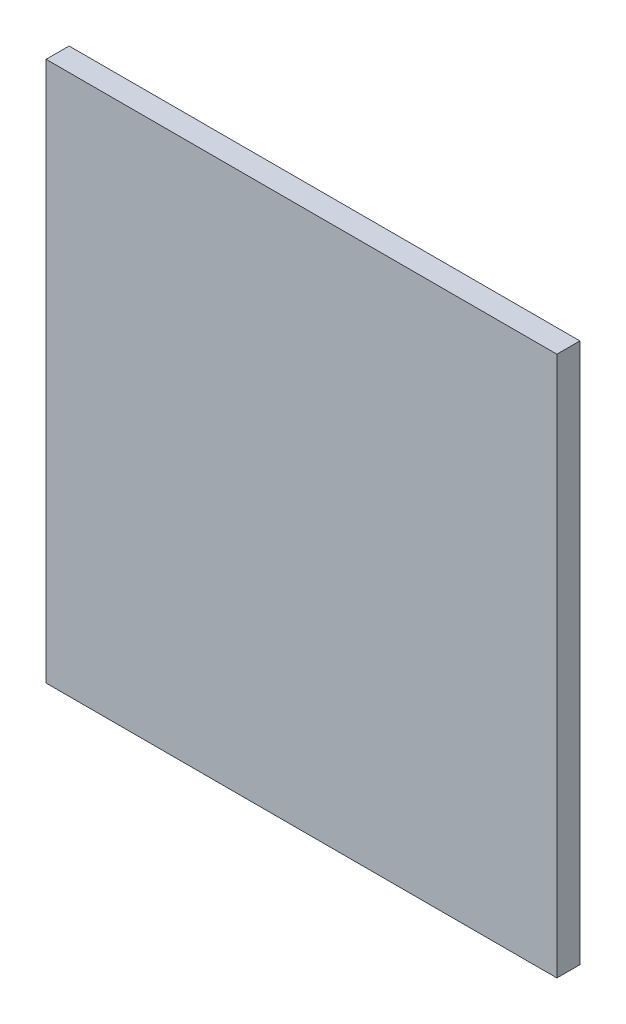
SolidWorks part; units mm, degrees
material "Glass"
ref_plane "Front" through (0, 0, 0) normal (0, 0, 1) x (1, 0, 0)
ref_plane "Top" through (0, 0, 0) normal (0, 1, 0) x (1, 0, 0)
ref_plane "Right" through (0, 0, 0) normal (1, 0, 0) x (0, 0, -1)
sketch "Sketch1" plane through (0, 0, 0) normal (0, 0, 1) x (1, 0, 0)
  line L1 (-27.75, -29.35) -> (27.75, -29.35)
  line L2 (-27.75, -29.35) -> (-27.75, 29.35)
  line L3 (-27.75, 29.35) -> (27.75, 29.35)
  line L4 (27.75, -29.35) -> (27.75, 29.35)
  line L5 (-27.75, -29.35) -> (27.75, 29.35) construction
  line L6 (-27.75, 29.35) -> (27.75, -29.35) construction
  point P0 (0, 0)
  dimension "D1" = 58.7
  dimension "D2" = 55.5
extrude "Boss-Extrude1" add sketch "Sketch1" along normal blind 2.5
